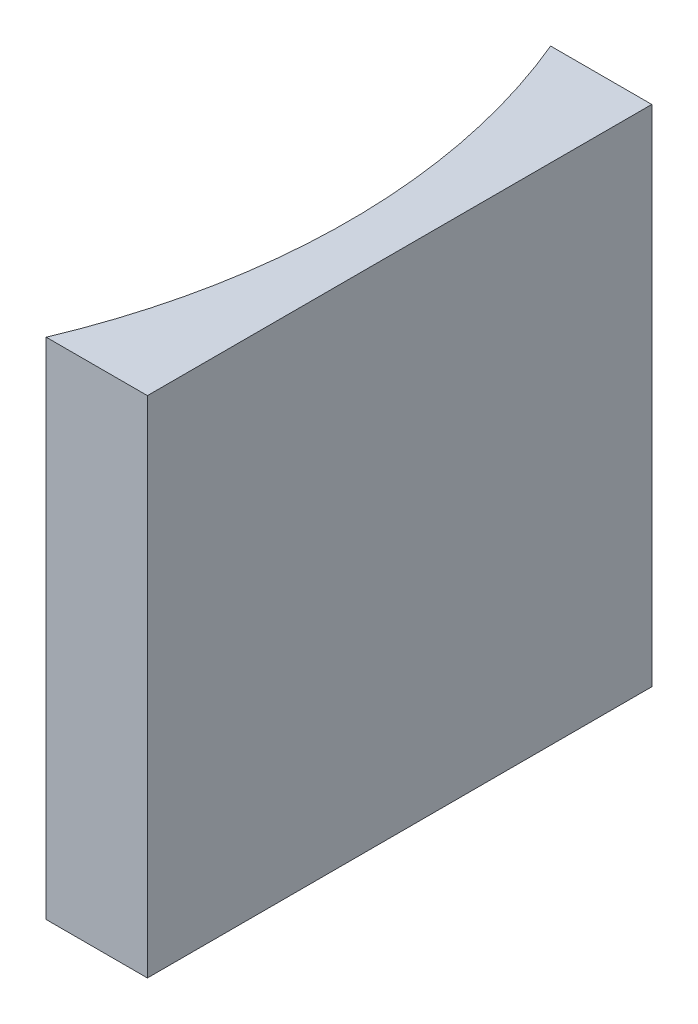
SolidWorks part; units mm, degrees
ref_plane "前视基准面" through (0, 0, 0) normal (0, 0, 1) x (1, 0, 0)
ref_plane "上视基准面" through (0, 0, 0) normal (0, 1, 0) x (1, 0, 0)
ref_plane "右视基准面" through (0, 0, 0) normal (1, 0, 0) x (0, 0, -1)
sketch "草图1" plane through (0, 0, 0) normal (0, 1, 0) x (1, 0, 0)
  line L0 (0, 0) -> (0, -20)
  line L1 (0, 0) -> (-4.0126, 0)
  line L2 (0, -20) -> (-4.0126, -20)
  line L3 (8.2336, -10) -> (-10.4405, -10) construction
  arc A0 (-4.0126, -20) -> (-4.0126, 0) centre (-27.85, -10) ccw
  point P7 (-2, -10)
  point P8 (0, -10)
  dimension "D2" = 25.85
  dimension "D3" = 2
  dimension "D1" = 20
extrude "凸台-拉伸1" add sketch "草图1" along normal blind 20
